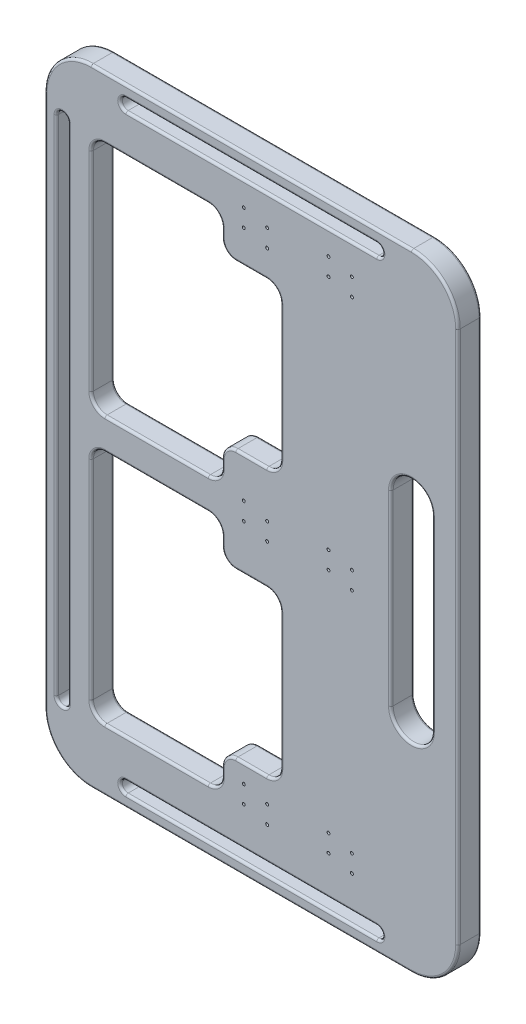
SolidWorks part; units mm, degrees
material "PVC Rigid"
ref_plane "Front Plane" through (0, 0, 0) normal (0, 0, 1) x (1, 0, 0)
ref_plane "Top Plane" through (0, 0, 0) normal (0, 1, 0) x (1, 0, 0)
ref_plane "Right Plane" through (0, 0, 0) normal (1, 0, 0) x (0, 0, -1)
sketch "Sketch1" plane through (0, 0, 0) normal (0, 0, 1) x (1, 0, 0)
  line L0 (9.525, -337.1515) -> (0, -337.1515) construction
  line L3 (4.7625, -385.4251) -> (4.7625, -288.878) construction
  line L7 (178.8413, 5.8307) -> (-169.3163, 5.8307)
  line L8 (229.3467, -44.6747) -> (229.3467, -624.1674)
  line L9 (178.8413, -674.6729) -> (-169.3163, -674.6729)
  line L10 (-219.8217, -44.6747) -> (-219.8217, -624.1674)
  line L11 (229.3467, -334.4211) -> (-219.8217, -334.4211) construction
  line L12 (178.8413, 5.8307) -> (178.8413, -674.6729) construction
  line L13 (178.8413, -232.8211) -> (178.8413, -436.0211) construction
  line L14 (201.2772, -232.8211) -> (201.2772, -436.0211)
  line L15 (156.4054, -232.8211) -> (156.4054, -436.0211)
  line L16 (-131.5196, -13.2193) -> (141.0446, -13.2193) construction
  line L17 (-42.0217, -61.0845) -> (-154.3708, -61.0845)
  line L18 (-27.0763, -76.0299) -> (-27.0763, -85.6213)
  line L19 (-42.0217, -317.5) -> (-154.3708, -317.5)
  line L20 (-169.3163, -76.0299) -> (-169.3163, -302.5546)
  line L23 (-131.5196, -6.8693) -> (141.0446, -6.8693)
  line L24 (-131.5196, -19.5693) -> (141.0446, -19.5693)
  line L28 (-169.3163, 5.8307) -> (-169.3163, -334.4211) construction
  line L30 (-27.0763, -292.9631) -> (-27.0763, -302.5546)
  line L31 (-12.1308, -100.5668) -> (21.4783, -100.5668)
  line L33 (-12.1308, -278.0177) -> (21.4783, -278.0177)
  line L34 (36.4237, -115.5122) -> (36.4237, -263.0723)
  line L35 (-27.0763, -375.879) -> (-27.0763, -366.2876)
  line L36 (-42.0217, -351.3421) -> (-154.3708, -351.3421)
  line L37 (-169.3163, -592.8122) -> (-169.3163, -366.2876)
  line L38 (-42.0217, -607.7577) -> (-154.3708, -607.7577)
  line L39 (-27.0763, -592.8122) -> (-27.0763, -583.2208)
  line L40 (-12.1308, -568.2754) -> (21.4783, -568.2754)
  line L41 (36.4237, -553.3299) -> (36.4237, -405.7699)
  line L42 (-12.1308, -390.8244) -> (21.4783, -390.8244)
  line L43 (-200.7717, -607.7577) -> (-200.7717, -61.0845) construction
  line L44 (-207.1217, -607.7577) -> (-207.1217, -61.0845)
  line L45 (-194.4217, -607.7577) -> (-194.4217, -61.0845)
  line L46 (-131.5196, -655.6229) -> (141.0446, -655.6229) construction
  line L47 (-131.5196, -661.9729) -> (141.0446, -661.9729)
  line L48 (-131.5196, -649.2729) -> (141.0446, -649.2729)
  arc A0 (-169.3163, -674.6729) -> (-219.8217, -624.1674) centre (-169.3163, -624.1674) cw
  arc A1 (229.3467, -624.1674) -> (178.8413, -674.6729) centre (178.8413, -624.1674) cw
  arc A2 (178.8413, 5.8307) -> (229.3467, -44.6747) centre (178.8413, -44.6747) cw
  arc A3 (-169.3163, 5.8307) -> (-219.8217, -44.6747) centre (-169.3163, -44.6747) ccw
  arc A4 (201.2772, -232.8211) -> (156.4054, -232.8211) centre (178.8413, -232.8211) ccw
  arc A5 (156.4054, -436.0211) -> (201.2772, -436.0211) centre (178.8413, -436.0211) ccw
  arc A6 (-131.5196, -6.8693) -> (-131.5196, -19.5693) centre (-131.5196, -13.2193) ccw
  arc A7 (141.0446, -19.5693) -> (141.0446, -6.8693) centre (141.0446, -13.2193) ccw
  arc A10 (21.4783, -100.5668) -> (36.4237, -115.5122) centre (21.4783, -115.5122) cw
  arc A11 (21.4783, -278.0177) -> (36.4237, -263.0723) centre (21.4783, -263.0723) ccw
  arc A12 (-27.0763, -292.9631) -> (-12.1308, -278.0177) centre (-12.1308, -292.9631) cw
  arc A13 (-27.0763, -302.5546) -> (-42.0217, -317.5) centre (-42.0217, -302.5546) cw
  arc A14 (-154.3708, -317.5) -> (-169.3163, -302.5546) centre (-154.3708, -302.5546) cw
  arc A15 (-154.3708, -61.0845) -> (-169.3163, -76.0299) centre (-154.3708, -76.0299) ccw
  arc A16 (-42.0217, -61.0845) -> (-27.0763, -76.0299) centre (-42.0217, -76.0299) cw
  arc A17 (-27.0763, -85.6213) -> (-12.1308, -100.5668) centre (-12.1308, -85.6213) ccw
  arc A18 (-27.0763, -366.2876) -> (-42.0217, -351.3421) centre (-42.0217, -366.2876) ccw
  arc A19 (-154.3708, -351.3421) -> (-169.3163, -366.2876) centre (-154.3708, -366.2876) ccw
  arc A20 (-154.3708, -607.7577) -> (-169.3163, -592.8122) centre (-154.3708, -592.8122) cw
  arc A21 (-42.0217, -607.7577) -> (-27.0763, -592.8122) centre (-42.0217, -592.8122) ccw
  arc A22 (-27.0763, -583.2208) -> (-12.1308, -568.2754) centre (-12.1308, -583.2208) cw
  arc A23 (21.4783, -568.2754) -> (36.4237, -553.3299) centre (21.4783, -553.3299) ccw
  arc A24 (21.4783, -390.8244) -> (36.4237, -405.7699) centre (21.4783, -405.7699) cw
  arc A25 (-27.0763, -375.879) -> (-12.1308, -390.8244) centre (-12.1308, -375.879) ccw
  arc A26 (-207.1217, -607.7577) -> (-194.4217, -607.7577) centre (-200.7717, -607.7577) ccw
  arc A27 (-194.4217, -61.0845) -> (-207.1217, -61.0845) centre (-200.7717, -61.0845) ccw
  arc A28 (-131.5196, -661.9729) -> (-131.5196, -649.2729) centre (-131.5196, -655.6229) cw
  arc A29 (141.0446, -649.2729) -> (141.0446, -661.9729) centre (141.0446, -655.6229) cw
  point P12 (4.7625, -337.1515)
  point P31 (178.8413, -334.4211)
  point P47 (4.7625, -13.2193)
  point P53 (4.7625, -38.6193)
  point P64 (36.4237, -100.5668)
  point P65 (-27.0763, -189.2922)
  point P78 (-169.3163, -61.0845)
  point P81 (-27.0763, -61.0845)
  point P84 (-27.0763, -100.5668)
  point P111 (-200.7717, -334.4211)
  point P118 (4.7625, -655.6229)
  point P125 (4.7625, -630.2229)
  dimension "D1" = 50.5054
  dimension "D7" = 14.9454
  dimension "D2" = 203.2
  dimension "D3" = 12.7
  dimension "D5" = 142.24
  dimension "D6" = 63.5
  dimension "D8" = 12.7
  dimension "D9" = 12.7
  dimension "D10" = 12.7
extrude "Boss-Extrude1" add sketch "Sketch1" along normal blind 25.4
fillet "Fillet1" radius 2.54 112 edges at (147.3946, -655.6229, 0) (4.7625, -661.9729, 0) (-137.8696, -655.6229, 0) (4.7625, -649.2729, 0) (-200.7717, -54.7345, 0) (-194.4217, -334.4211, 0) (-200.7717, -614.1077, 0) (-207.1217, -334.4211, 0) (32.0463, -395.2018, 0) (36.4237, -479.5499, 0) (32.0463, -563.8979, 0) (4.6737, -568.2754, 0) (-22.6989, -572.6528, 0) (-27.0763, -588.0165, 0) (-31.4537, -603.3802, 0) (-98.1963, -607.7577, 0) (-164.9389, -603.3802, 0) (-169.3163, -479.5499, 0) (-164.9389, -355.7195, 0) (-98.1963, -351.3421, 0) (-31.4537, -355.7195, 0) (-27.0763, -371.0833, 0) (-22.6989, -386.447, 0) (4.6737, -390.8244, 0) (32.0463, -273.6403, 0) (4.6737, -278.0177, 0) (-22.6989, -282.3951, 0) (-27.0763, -297.7588, 0) (-31.4537, -313.1226, 0) (-98.1963, -317.5, 0) (-164.9389, -313.1226, 0) (-169.3163, -189.2922, 0) (-164.9389, -65.4619, 0) (-98.1963, -61.0845, 0) (-31.4537, -65.4619, 0) (-27.0763, -80.8256, 0) (-22.6989, -96.1893, 0) (4.6737, -100.5668, 0) (32.0463, -104.9442, 0) (36.4237, -189.2922, 0) (147.3946, -13.2193, 0) (4.7625, -19.5693, 0) (-137.8696, -13.2193, 0) (4.7625, -6.8693, 0) (178.8413, -458.457, 0) (156.4054, -334.4211, 0) (178.8413, -210.3852, 0) (201.2772, -334.4211, 0) (4.7625, -674.6729, 0) (214.554, -659.8802, 0) (229.3467, -334.4211, 0) (214.554, -8.962, 0) (4.7625, 5.8307, 0) (-205.029, -8.962, 0) (-219.8217, -334.4211, 0) (-205.029, -659.8802, 0) (-194.4217, -334.4211, 25.4) (-200.7717, -54.7345, 25.4) (-207.1217, -334.4211, 25.4) (-200.7717, -614.1077, 25.4) (4.6737, -100.5668, 25.4) (-22.6989, -96.1893, 25.4) (-27.0763, -80.8256, 25.4) (-31.4537, -65.4619, 25.4) (-98.1963, -61.0845, 25.4) (-164.9389, -65.4619, 25.4) (-169.3163, -189.2922, 25.4) (-164.9389, -313.1226, 25.4) (-98.1963, -317.5, 25.4) (-31.4537, -313.1226, 25.4) (-27.0763, -297.7588, 25.4) (-22.6989, -282.3951, 25.4) (4.6737, -278.0177, 25.4) (32.0463, -273.6403, 25.4) (36.4237, -189.2922, 25.4) (32.0463, -104.9442, 25.4) (4.7625, -19.5693, 25.4) (147.3946, -13.2193, 25.4) (4.7625, -6.8693, 25.4) (-137.8696, -13.2193, 25.4) (-219.8217, -334.4211, 25.4) (-205.029, -8.962, 25.4) (4.7625, 5.8307, 25.4) (214.554, -8.962, 25.4) (229.3467, -334.4211, 25.4) (214.554, -659.8802, 25.4) (4.7625, -674.6729, 25.4) (-205.029, -659.8802, 25.4) (156.4054, -334.4211, 25.4) (178.8413, -458.457, 25.4) (201.2772, -334.4211, 25.4) (178.8413, -210.3852, 25.4) (-27.0763, -371.0833, 25.4) (-31.4537, -355.7195, 25.4) (-98.1963, -351.3421, 25.4) (-164.9389, -355.7195, 25.4) (-169.3163, -479.5499, 25.4) (-164.9389, -603.3802, 25.4) (-98.1963, -607.7577, 25.4) (-31.4537, -603.3802, 25.4) (-27.0763, -588.0165, 25.4) (-22.6989, -572.6528, 25.4) (4.6737, -568.2754, 25.4) (32.0463, -563.8979, 25.4) (36.4237, -479.5499, 25.4) (32.0463, -395.2018, 25.4) (4.6737, -390.8244, 25.4) (-22.6989, -386.447, 25.4) (4.7625, -661.9729, 25.4) (147.3946, -655.6229, 25.4) (4.7625, -649.2729, 25.4) (-137.8696, -655.6229, 25.4)
hole_wizard "Hole2" positions "Sketch9" profile "Sketch10" legacy
sketch "Sketch9" plane through (0, 0, 0) normal (0, 0, -1) x (-1, 0, 0)
  point P0 (-114.0534, -52.004)
  point P3 (-114.0534, -71.054)
  point P6 (-88.6534, -45.654)
  point P9 (-88.6534, -64.704)
  point P12 (3.4216, -45.654)
  point P15 (3.4216, -64.704)
  point P18 (-21.9784, -52.004)
  point P21 (-21.9784, -71.054)
  point P24 (-21.9784, -328.0711)
  point P27 (-21.9784, -347.1211)
  point P30 (3.4216, -340.7711)
  point P33 (3.4216, -321.7211)
  point P49 (-114.0534, -594.5702)
  point P52 (-114.0534, -613.6202)
  point P55 (-88.6534, -607.2702)
  point P58 (-88.6534, -588.2202)
  point P61 (3.4216, -588.2202)
  point P64 (3.4216, -607.2702)
  point P67 (-21.9784, -594.5702)
  point P70 (-21.9784, -613.6202)
  point P88 (-88.6534, -340.7711)
  point P91 (-88.6534, -321.7211)
  point P94 (-114.0534, -347.1211)
  point P97 (-114.0534, -328.0711)
sketch "Sketch10" plane through (114.0534, -52.004, 0) normal (1, 0, 0) x (0, 1, 0)
  line L0 (0, 0) -> (0, 31.75)
  line L1 (0, 31.75) -> (1.5875, 31.75)
  line L2 (1.5875, 31.75) -> (1.5875, 3.5052)
  line L3 (1.5875, 3.5052) -> (2.8702, 3.5052)
  line L4 (2.8702, 3.5052) -> (2.8702, 0)
  line L5 (2.8702, 0) -> (0, 0)
  line L6 (0, 110) -> (0, -10) construction
  dimension "Diameter" = 3.175
  dimension "Depth" = 31.75
  dimension "C-Bore Diameter" = 5.7404
  dimension "C-Bore Depth" = 3.5052
